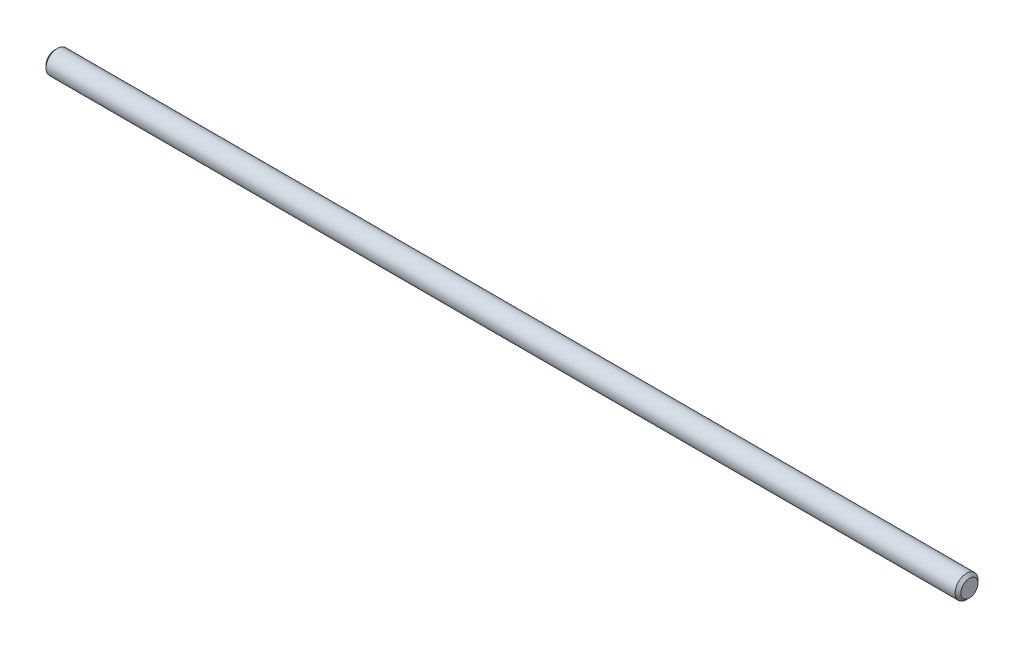
SolidWorks part; units mm, degrees
ref_plane "Front Plane" through (0, 0, 0) normal (0, 0, 1) x (1, 0, 0)
ref_plane "Top Plane" through (0, 0, 0) normal (0, 1, 0) x (1, 0, 0)
ref_plane "Right Plane" through (0, 0, 0) normal (1, 0, 0) x (0, 0, -1)
sketch "Sketch2" plane through (0, 0, 0) normal (1, 0, 0) x (0, 0, -1)
  circle A0 centre (0, 0) radius 2
  dimension "D1" = 4
extrude "Boss-Extrude2" add sketch "Sketch2" along normal blind 160
chamfer "Chamfer2" distance 0.5 angle 45 2 edges at (0, 0, -2) (160, 0, -2)
